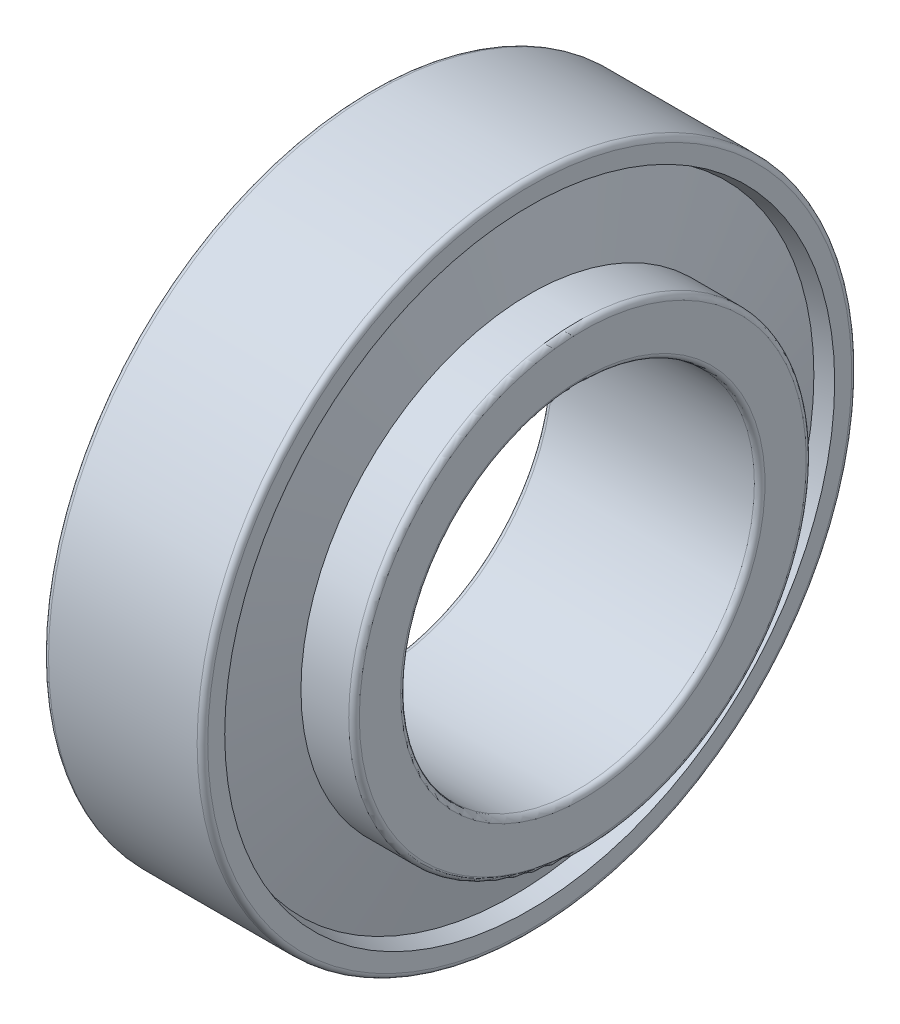
SolidWorks part; units mm, degrees
material "AISI Тип A2 Инструментальная сталь"
ref_plane "Спереди" through (0, 0, 0) normal (0, 0, 1) x (1, 0, 0)
ref_plane "Сверху" through (0, 0, 0) normal (0, 1, 0) x (1, 0, 0)
ref_plane "Справа" through (0, 0, 0) normal (1, 0, 0) x (0, 0, -1)
sketch "Эскиз1" plane through (0, 0, 0) normal (0, 0, 1) x (1, 0, 0)
  line L20 (-882.5277, 0) -> (43243.8573, 0) construction
  line L33 (0.7557, 15.0145) -> (0, 14.8105)
  line L34 (0, 14.8105) -> (0, 18.2)
  line L35 (0.3, 18.5) -> (8.7, 18.5)
  line L36 (9, 18.2) -> (9, 17.2403)
  line L37 (9, 17.2403) -> (8.0734, 16.9901)
  line L38 (0.7557, 15.0145) -> (8.0734, 16.9901) construction
  line L39 (1.5114, 11.4593) -> (0, 11.4593)
  line L40 (0, 11.4593) -> (0, 10.3)
  line L41 (0.3, 10) -> (11.7, 10)
  line L42 (12, 10.3) -> (12, 12.6309)
  line L43 (11.7, 12.9309) -> (9, 12.9309)
  line L44 (9, 12.9309) -> (9, 12.6309)
  line L45 (1.5114, 11.4593) -> (9, 12.6309) construction
  line L46 (9, 12.6309) -> (8.0734, 16.9901)
  line L47 (1.5114, 11.4593) -> (0.7557, 15.0145)
  line L48 (1.1335, 13.2369) -> (8.5367, 14.8105) construction
  line L49 (0, 14.8105) -> (8.5367, 14.8105) construction
  line L50 (0.7557, 15.0145) -> (0.7557, 11.4593) construction
  arc A0 (0, 18.2) -> (0.3, 18.5) centre (0.3, 18.2) cw
  arc A1 (8.7, 18.5) -> (9, 18.2) centre (8.7, 18.2) cw
  arc A2 (0, 10.3) -> (0.3, 10) centre (0.3, 10.3) ccw
  arc A3 (12, 10.3) -> (11.7, 10) centre (11.7, 10.3) cw
  arc A4 (11.7, 12.9309) -> (12, 12.6309) centre (11.7, 12.6309) cw
  point P12 (8.5367, 14.8105)
  dimension "гост r1" = 0.3
  dimension "гост r2" = 0.3
  dimension "гост DD" = 37
  dimension "гост B" = 12
  dimension "гост C" = 9
  dimension "гост T" = 12
  dimension "гост E" = 29.621
  dimension "гост d" = 20
  dimension "гост alfa" = 12
revolve "Повернуть1" add sketch "Эскиз1" angle 360 about L20
